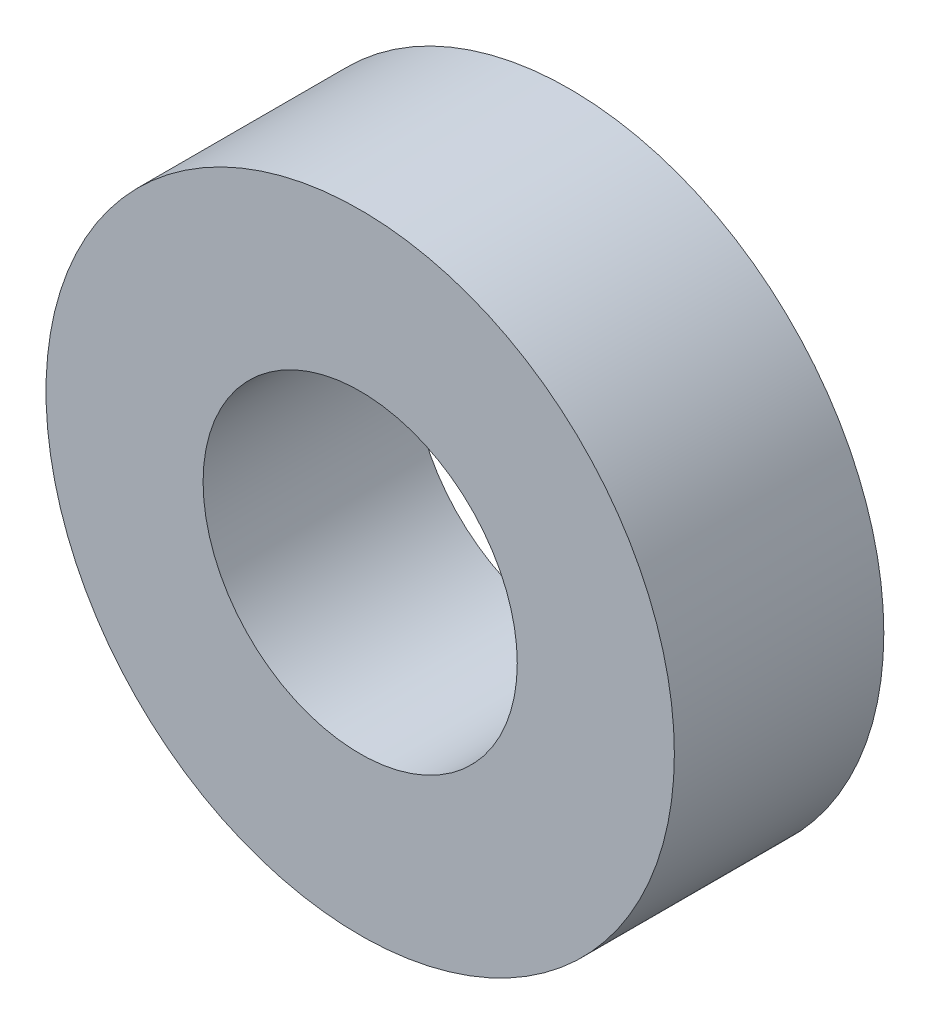
SolidWorks part; units mm, degrees
ref_plane "Plan de face" through (0, 0, 0) normal (0, 0, 1) x (1, 0, 0)
ref_plane "Plan de dessus" through (0, 0, 0) normal (0, 1, 0) x (1, 0, 0)
ref_plane "Plan de droite" through (0, 0, 0) normal (1, 0, 0) x (0, 0, -1)
sketch "Esquisse1" plane through (0, 0, 0) normal (0, 0, 1) x (1, 0, 0)
  circle A0 centre (0, 0) radius 3
  circle A1 centre (0, 0) radius 6
extrude "Extrusion1" add sketch "Esquisse1" along normal blind 4
